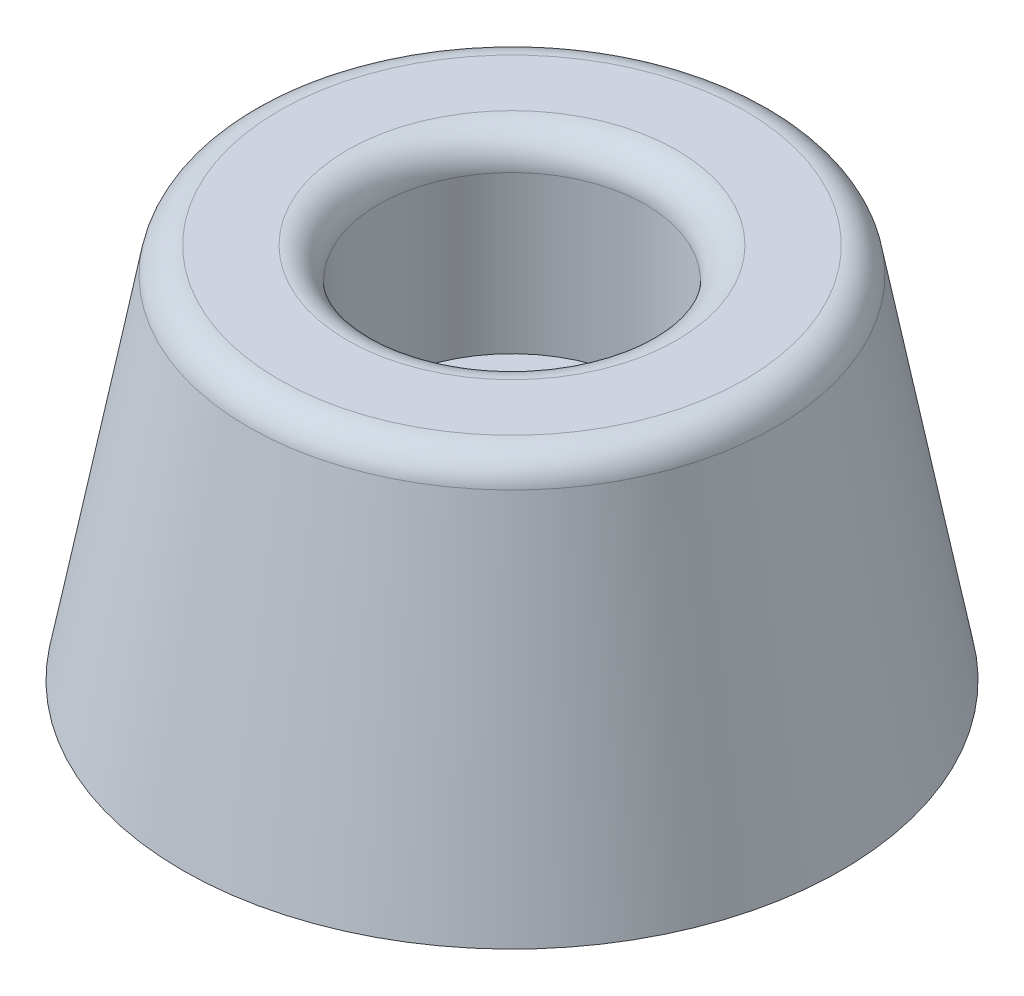
SolidWorks part; units mm, degrees
ref_plane "Front Plane" through (0, 0, 0) normal (0, 0, 1) x (1, 0, 0)
ref_plane "Top Plane" through (0, 0, 0) normal (0, 1, 0) x (1, 0, 0)
ref_plane "Right Plane" through (0, 0, 0) normal (1, 0, 0) x (0, 0, -1)
sketch "Sketch1" plane through (0, 0, 0) normal (1, 0, 0) x (0, 0, -1)
  line L0 (2.1, 6) -> (4.25, 6)
  line L1 (4.25, 6) -> (4.25, 12)
  line L2 (4.25, 12) -> (8.25, 12)
  line L3 (8.25, 12) -> (10.5, 0)
  line L4 (10.5, 0) -> (2.1, 0)
  line L5 (2.1, 0) -> (2.1, 6)
  line L6 (0, 0) -> (0, 21.3376) construction
  dimension "D1" = 6
  dimension "D2" = 12
  dimension "D3" = 21
  dimension "D4" = 16.5
  dimension "D5" = 4.2
  dimension "D6" = 8.5
revolve "Revolve1" add sketch "Sketch1" angle 360 about L6
fillet "Fillet1" radius 1 2 edges at (0, 12, -8.25) (0, 12, -4.25)
